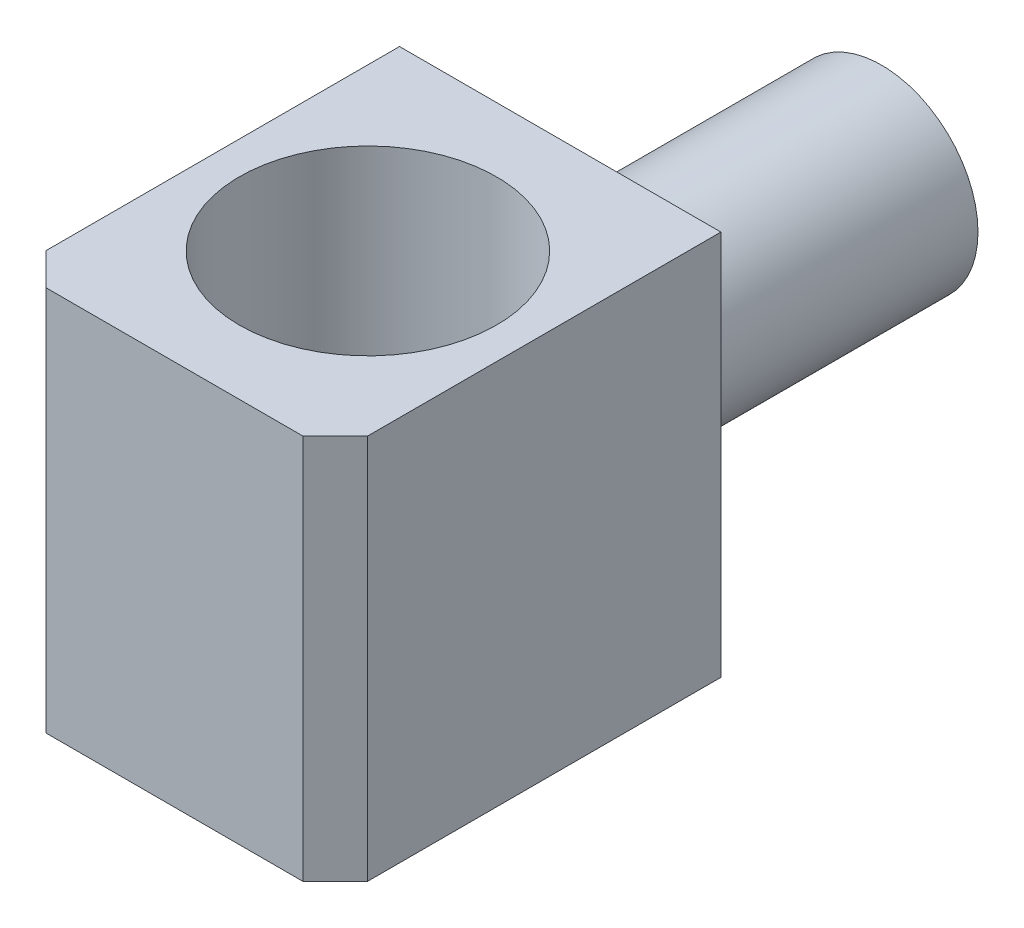
SolidWorks part; units mm, degrees
ref_plane "Alzado" through (0, 0, 0) normal (0, 0, 1) x (1, 0, 0)
ref_plane "Planta" through (0, 0, 0) normal (0, 1, 0) x (1, 0, 0)
ref_plane "Vista lateral" through (0, 0, 0) normal (1, 0, 0) x (0, 0, -1)
sketch "Croquis1" plane through (0, 0, 0) normal (0, 1, 0) x (1, 0, 0)
  line L0 (0, 0) -> (0, -12)
  line L1 (0, -12) -> (10, -12)
  line L2 (10, -12) -> (10, 0)
  line L3 (10, 0) -> (0, 0)
  line L4 (0, -6) -> (5.0166, -6) construction
  line L5 (5.0166, -6) -> (5, 0) construction
  circle A0 centre (5.0166, -6) radius 4
extrude "Saliente-Extruir1" add sketch "Croquis1" along normal blind 12
chamfer "Chaflán1" distance 1 angle 45 2 edges at (10, 6, 12) (0, 6, 12)
sketch "Croquis2" plane through (0, 0, 0) normal (0, 0, -1) x (-1, 0, 0)
  line L0 (-5, 12) -> (-5, 0) construction
  line L3 (-10, 12) -> (0, 12) construction
  line L4 (-10, 0) -> (0, 0) construction
  circle A0 centre (-5, 6) radius 3
extrude "Saliente-Extruir2" add sketch "Croquis2" along normal blind 10
